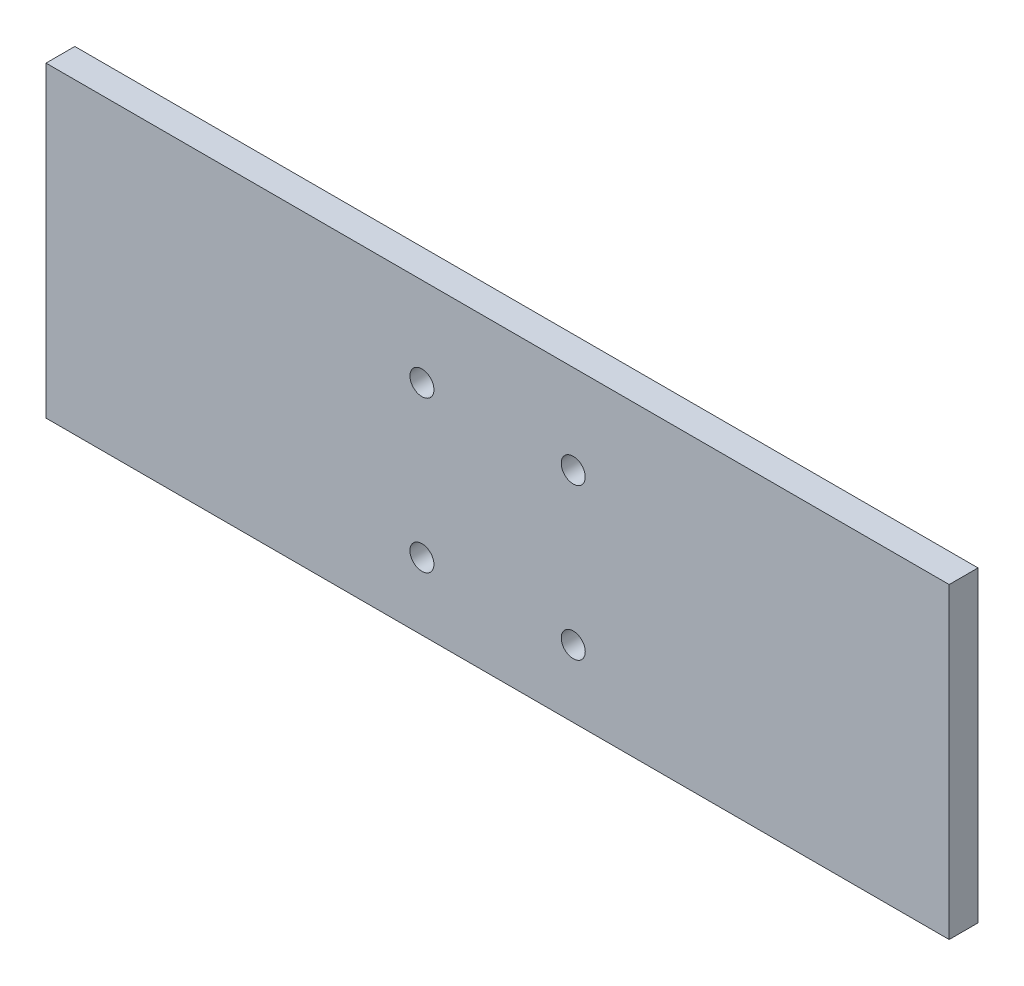
SolidWorks part; units mm, degrees
ref_plane "Front Plane" through (0, 0, 0) normal (0, 0, 1) x (1, 0, 0)
ref_plane "Top Plane" through (0, 0, 0) normal (0, 1, 0) x (1, 0, 0)
ref_plane "Right Plane" through (0, 0, 0) normal (1, 0, 0) x (0, 0, -1)
sketch "Sketch1" plane through (0, 0, 0) normal (0, 0, 1) x (1, 0, 0)
  line L1 (298.45, 101.6) -> (-298.45, 101.6)
  line L2 (298.45, 101.6) -> (298.45, -101.6)
  line L3 (298.45, -101.6) -> (-298.45, -101.6)
  line L4 (-298.45, 101.6) -> (-298.45, -101.6)
  line L5 (298.45, 101.6) -> (-298.45, -101.6) construction
  line L6 (298.45, -101.6) -> (-298.45, 101.6) construction
  point P0 (0, 0)
  dimension "D1" = 596.9
  dimension "D2" = 203.2
extrude "Boss-Extrude1" add sketch "Sketch1" along normal mid plane 19.05
sketch "Sketch2" plane through (0, 0, 9.525) normal (0, 0, 1) x (1, 0, 0)
  line L0 (-298.45, -101.6) -> (298.45, -101.6) construction
  line L2 (0, 0) -> (0, 101.6) construction
  line L3 (298.45, 101.6) -> (-298.45, 101.6) construction
  circle A0 centre (-50, 42.85) radius 7.9375
  circle A1 centre (-50, -57.15) radius 7.9375
  circle A2 centre (50, 42.85) radius 7.9375
  circle A3 centre (50, -57.15) radius 7.9375
  dimension "D1" = 100
  dimension "D2" = 100
  dimension "D3" = 15.875
  dimension "D4" = 44.45
extrude "Cut-Extrude1" cut sketch "Sketch2" against normal through all
